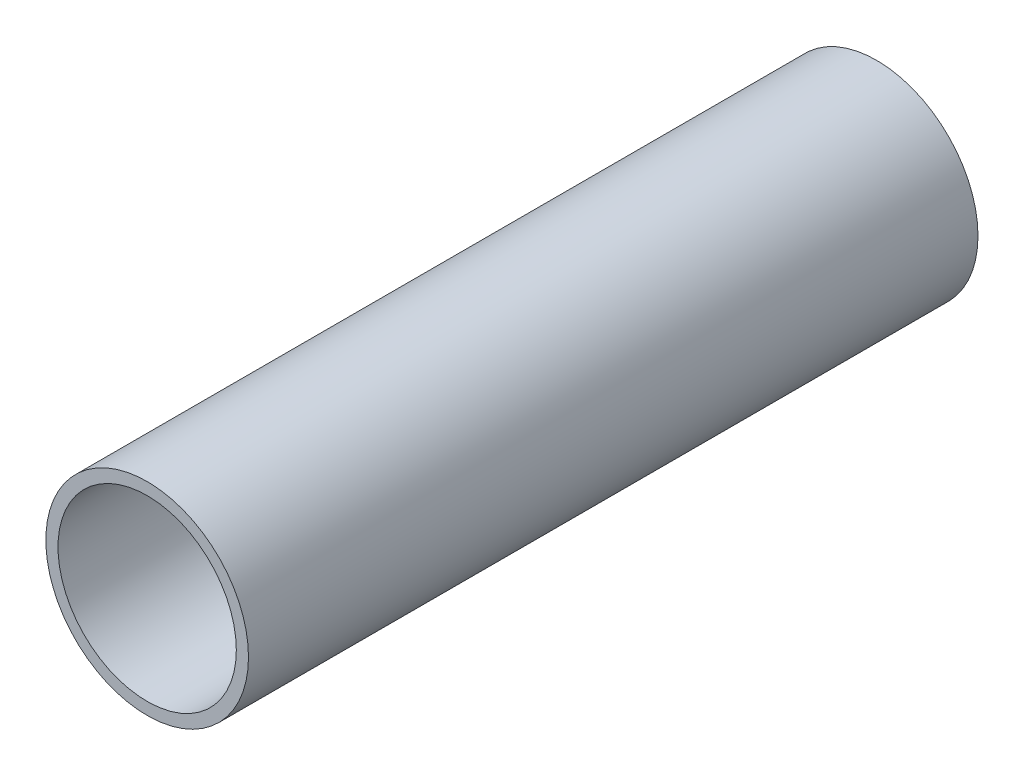
SolidWorks part; units mm, degrees
material "Carbon Fiber Tube - UD Approx"
ref_plane "Front Plane" through (0, 0, 0) normal (0, 0, 1) x (1, 0, 0)
ref_plane "Top Plane" through (0, 0, 0) normal (0, 1, 0) x (1, 0, 0)
ref_plane "Right Plane" through (0, 0, 0) normal (1, 0, 0) x (0, 0, -1)
sketch "Sketch1" plane through (0, 0, 0) normal (0, 0, 1) x (1, 0, 0)
  circle A0 centre (0, 0) radius 12.5
  circle A1 centre (0, 0) radius 11
  dimension "D1" = 25
  dimension "D2" = 22
extrude "Boss-Extrude1" add sketch "Sketch1" along normal blind 90
